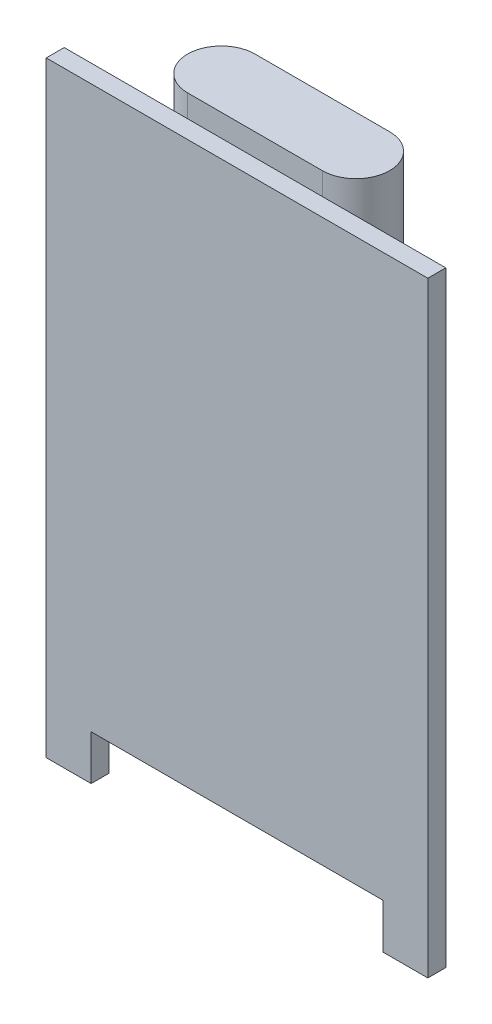
SolidWorks part; units mm, degrees
ref_plane "Plano frontal" through (0, 0, 0) normal (0, 0, 1) x (1, 0, 0)
ref_plane "Plano superior" through (0, 0, 0) normal (0, 1, 0) x (1, 0, 0)
ref_plane "Plano direito" through (0, 0, 0) normal (1, 0, 0) x (0, 0, -1)
sketch "Esboço1" plane through (0, 0, 0) normal (0, 0, 1) x (1, 0, 0)
  line L1 (-8.5, 13.5) -> (8.5, 13.5)
  line L2 (-8.5, 13.5) -> (-8.5, -13.5)
  line L3 (-8.5, -13.5) -> (8.5, -13.5)
  line L4 (8.5, 13.5) -> (8.5, -13.5)
  line L5 (-8.5, 13.5) -> (8.5, -13.5) construction
  line L6 (-8.5, -13.5) -> (8.5, 13.5) construction
  line L7 (-6.5, -11.5) -> (6.5, -11.5)
  line L8 (-6.5, -11.5) -> (-6.5, -13.5)
  line L9 (-6.5, -13.5) -> (6.5, -13.5)
  line L10 (6.5, -11.5) -> (6.5, -13.5)
  line L11 (-6.5, -11.5) -> (6.5, -13.5) construction
  line L12 (-6.5, -13.5) -> (6.5, -11.5) construction
  point P0 (0, 0)
  point P6 (0, -12.5)
  point P11 (0, 0)
  dimension "D1" = 27
  dimension "D2" = 17
  dimension "D3" = 2
  dimension "D4" = 13
extrude "Ressalto-extrusão1" add sketch "Esboço1" along normal blind 0.8 contours L7 L10 L3 L4 L1 L2 L8
sketch "Esboço3" plane through (0, 13.5, 0) normal (0, 1, 0) x (1, 0, 0)
  line L0 (-3, 1.5) -> (3, 1.5) construction
  line L1 (-3, 3) -> (3, 3)
  line L2 (-3, 0) -> (3, 0)
  line L3 (-8.5, 0) -> (8.5, 0) construction
  arc A0 (-3, 3) -> (-3, 0) centre (-3, 1.5) ccw
  arc A1 (3, 0) -> (3, 3) centre (3, 1.5) ccw
  point P2 (0, 1.5)
  point P9 (0, 0)
  dimension "D1" = 9
  dimension "D2" = 1.5
extrude "Ressalto-extrusão2" add sketch "Esboço3" along normal blind 1 and the other way blind 6
